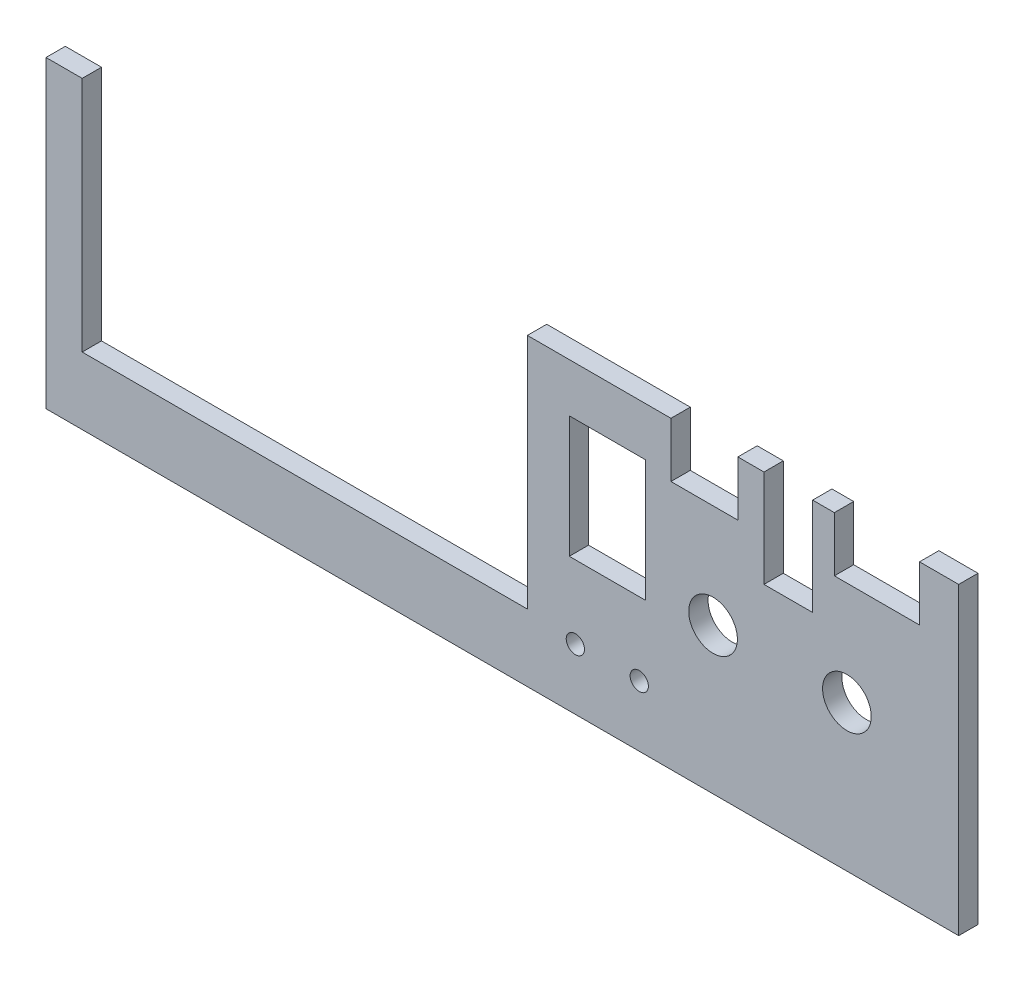
SolidWorks part; units mm, degrees
ref_plane "Front Plane" through (0, 0, 0) normal (0, 0, 1) x (1, 0, 0)
ref_plane "Top Plane" through (0, 0, 0) normal (0, 1, 0) x (1, 0, 0)
ref_plane "Right Plane" through (0, 0, 0) normal (1, 0, 0) x (0, 0, -1)
sketch "Sketch2" plane through (0, 0, 0) normal (0, 0, 1) x (1, 0, 0)
  line L16 (24.7414, 42) -> (12.2414, 42)
  line L17 (24.7414, 22) -> (24.7414, 42)
  line L18 (12.2414, 22) -> (24.7414, 22)
  line L19 (12.2414, 42) -> (12.2414, 22)
  line L56 (-71.7586, 50) -> (-71.7586, 2)
  line L57 (-71.7586, 2) -> (74.2414, 2)
  line L58 (74.2414, 2) -> (74.2414, 50)
  line L59 (74.2414, 50) -> (69.8083, 50)
  line L60 (69.8083, 50) -> (69.8083, 41)
  line L61 (69.8083, 41) -> (55.8083, 41)
  line L62 (55.8083, 41) -> (55.8083, 50)
  line L63 (55.8083, 50) -> (52.2414, 50)
  line L64 (52.2414, 50) -> (52.2414, 34)
  line L65 (52.2414, 34) -> (44.2414, 34)
  line L66 (44.2414, 34) -> (44.2414, 50)
  line L67 (44.2414, 50) -> (39.9531, 50)
  line L68 (39.9531, 50) -> (39.9531, 41)
  line L69 (39.9531, 41) -> (28.9531, 41)
  line L70 (28.9531, 41) -> (28.9531, 50)
  line L71 (28.9531, 50) -> (5.3584, 50)
  line L72 (5.3584, 50) -> (5.3584, 11.0459)
  line L73 (5.3584, 11.0459) -> (-67.8104, 11.0459)
  line L74 (-67.8104, 11.0459) -> (-67.8104, 50)
  line L75 (-67.8104, 50) -> (-71.7586, 50)
  circle A2 centre (23.7414, 10) radius 1.5
  circle A4 centre (13.2414, 10) radius 1.5
  circle A6 centre (57.8713, 24) radius 4
  circle A8 centre (35.8713, 24) radius 4
extrude "Boss-Extrude1" add sketch "Sketch2" along normal blind 3.175
sketch "Sketch3" plane through (0, 0, 0) normal (0, 0, -1) x (-1, 0, 0)
  line L0 (-74.2414, 50) -> (-69.8083, 50) construction
  line L1 (-76.2414, 50) -> (73.7586, 50)
  line L2 (-76.2414, 50) -> (-76.2414, 0)
  line L3 (-76.2414, 0) -> (73.7586, 0)
  line L4 (73.7586, 50) -> (73.7586, 0)
  line L5 (-74.2414, 2) -> (-74.2414, 50) construction
  line L6 (71.7586, 2) -> (-74.2414, 2) construction
  line L7 (71.7586, 50) -> (71.7586, 2) construction
  line L9 (-74.2414, 50) -> (71.7586, 50)
  line L10 (-74.2414, 50) -> (-74.2414, 2)
  line L11 (-74.2414, 2) -> (71.7586, 2)
  line L12 (71.7586, 50) -> (71.7586, 2)
  point P6 (-72.0249, 50)
  line M22 (-74.2414, 50) -> (-74.2414, 2)
  line M23 (-74.2414, 2) -> (71.7586, 2)
  line M24 (71.7586, 2) -> (71.7586, 50)
  dimension "D1" = 0
  dimension "D2" = 2
  dimension "D3" = 2
  dimension "D4" = 2
extrude "Boss-Extrude2" add sketch "Sketch3" against normal blind 3.175 contours L4 L1 L2 L3 M24 M23 M22
